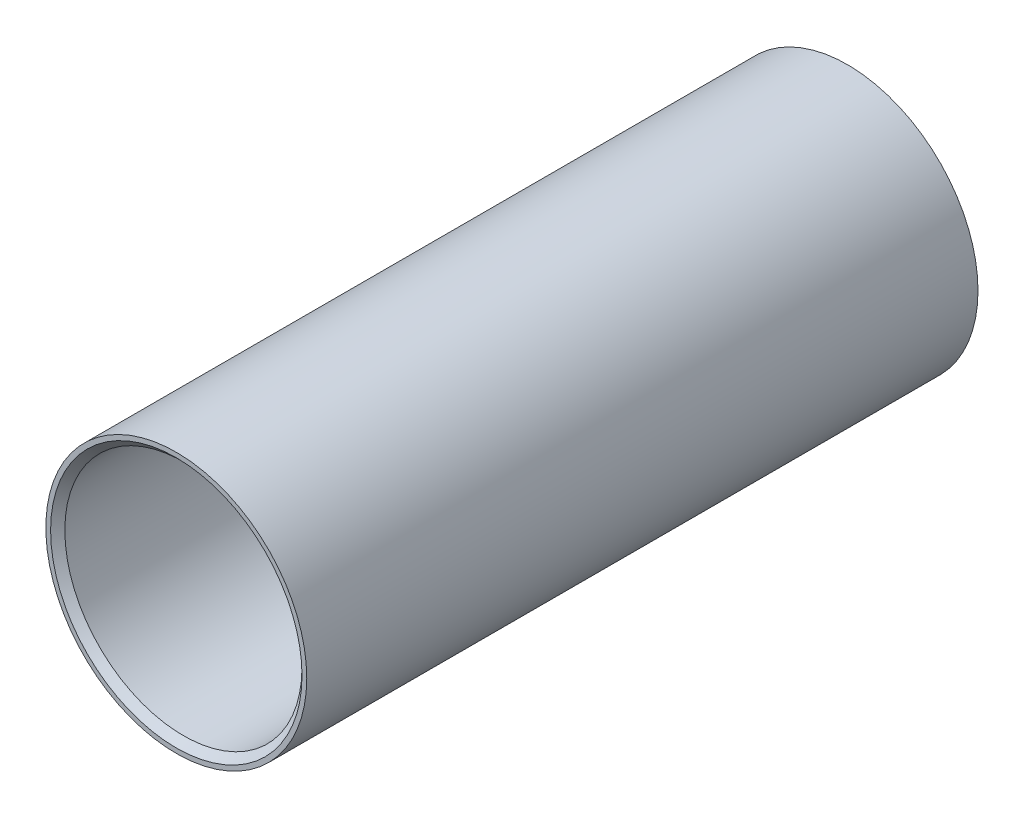
SolidWorks part; units mm, degrees
ref_plane "Front Plane" through (0, 0, 0) normal (0, 0, 1) x (1, 0, 0)
ref_plane "Top Plane" through (0, 0, 0) normal (0, 1, 0) x (1, 0, 0)
ref_plane "Right Plane" through (0, 0, 0) normal (1, 0, 0) x (0, 0, -1)
sketch "Sketch1" plane through (0, 0, 0) normal (1, 0, 0) x (0, 0, -1)
  line L0 (0, 0) -> (0, 6416.7499) construction
  line L1 (0, 0) -> (6416.7499, 0) construction
  line L3 (-14.15, 5.5) -> (14.15, 5.5)
  line L4 (-14.15, 5.5) -> (-14.15, 5.3)
  line L5 (-13.85, 5) -> (13.85, 5)
  line L6 (14.15, 5.5) -> (14.15, 5.3)
  line L7 (13.85, 5) -> (14.15, 5.3)
  line L8 (-14.15, 5.3) -> (-13.85, 5)
  point P6 (14.15, 5)
  point P16 (-14.15, 5)
  dimension "L" = 28.3
  dimension "D2" = 45
  dimension "Ø1" = 10
  dimension "Ø2" = 11
  dimension "C1" = 0.3
  dimension "D7" = 45
  dimension "C2" = 0.3
revolve "Revolve1" add sketch "Sketch1" angle 360 about L1
